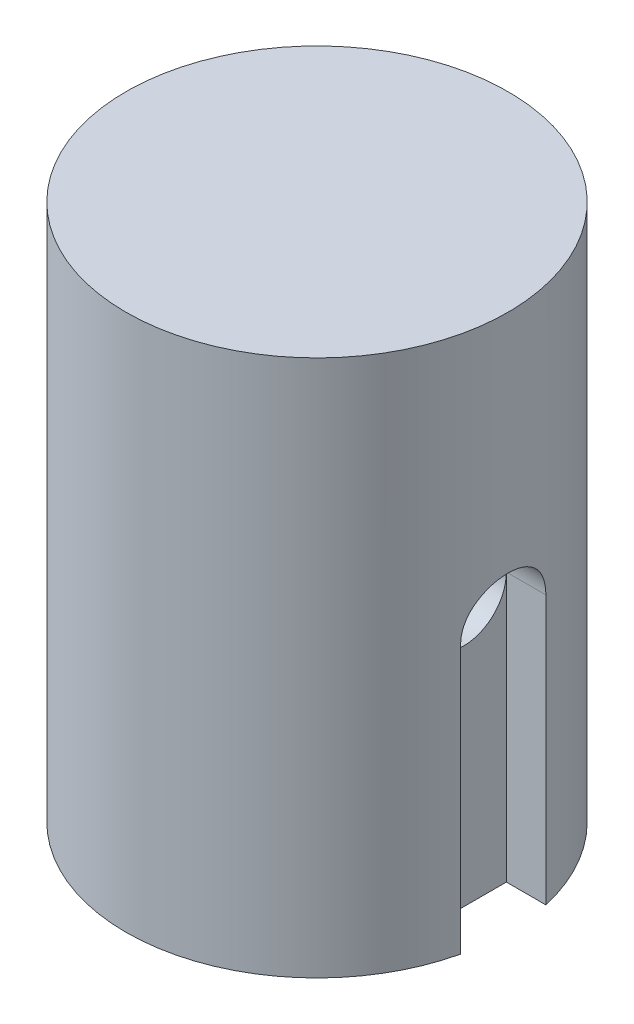
SolidWorks part; units mm, degrees
ref_plane "Front Plane" through (0, 0, 0) normal (0, 0, 1) x (1, 0, 0)
ref_plane "Top Plane" through (0, 0, 0) normal (0, 1, 0) x (1, 0, 0)
ref_plane "Right Plane" through (0, 0, 0) normal (1, 0, 0) x (0, 0, -1)
sketch "Sketch1" plane through (0, 0, 0) normal (0, 1, 0) x (1, 0, 0)
  circle A0 centre (0, 0) radius 8.895
  dimension "D1" = 17.79
extrude "Boss-Extrude1" add sketch "Sketch1" against normal blind 25
sketch "Sketch2" plane through (0, -25, 0) normal (0, -1, 0) x (1, 0, 0)
  line L0 (-6.8312, 1.9844) -> (-6.8312, -1.9844)
  line L1 (-6.8312, 1.9844) -> (-8.6708, 1.9844)
  line L2 (-6.8312, -1.9844) -> (-8.6708, -1.9844)
  line L3 (-8.895, 0) -> (-8.895, -1.1975) construction
  circle A0 centre (0, 0) radius 8.895 construction
  arc A1 (-8.6708, 1.9844) -> (-8.6708, -1.9844) centre (0, 0) ccw
  point P3 (-6.8313, 0)
  dimension "D2" = 3.9688
  dimension "D1" = 2.0637
extrude "Cut-Extrude1" cut sketch "Sketch2" against normal blind 12.5
mirror "Mirror1" about plane through (0, 0, 0) normal (1, 0, 0) of "Cut-Extrude1"
sketch "Sketch3" plane through (0, 0, 0) normal (1, 0, 0) x (0, 0, -1)
  line L0 (1.9844, -12.5) -> (-1.9844, -12.5) construction
  circle A0 centre (0, -12.5) radius 1.9844
extrude "Cut-Extrude2" cut sketch "Sketch3" against normal through all both and the other way through all
equation "\"D_SHOULDER\" = 17.79mm"
equation "\"OD_AIRF\"= 18.5mm"
equation "\"W_CORD\"= 3.175mm"
equation "\"L_SHOULDER\"= 25mm"
equation "\"L_CONE\"= 4in"
equation "\"D1@Sketch1\"=\"D_SHOULDER\""
equation "\"D1@Boss-Extrude1\"=\"L_SHOULDER\""
equation "\"D2@Sketch2\"=1.25*\"W_CORD\""
equation "\"D1@Sketch2\"=0.65*\"W_CORD\""
equation "\"D1@Cut-Extrude1\"=\"L_SHOULDER\"/2"
